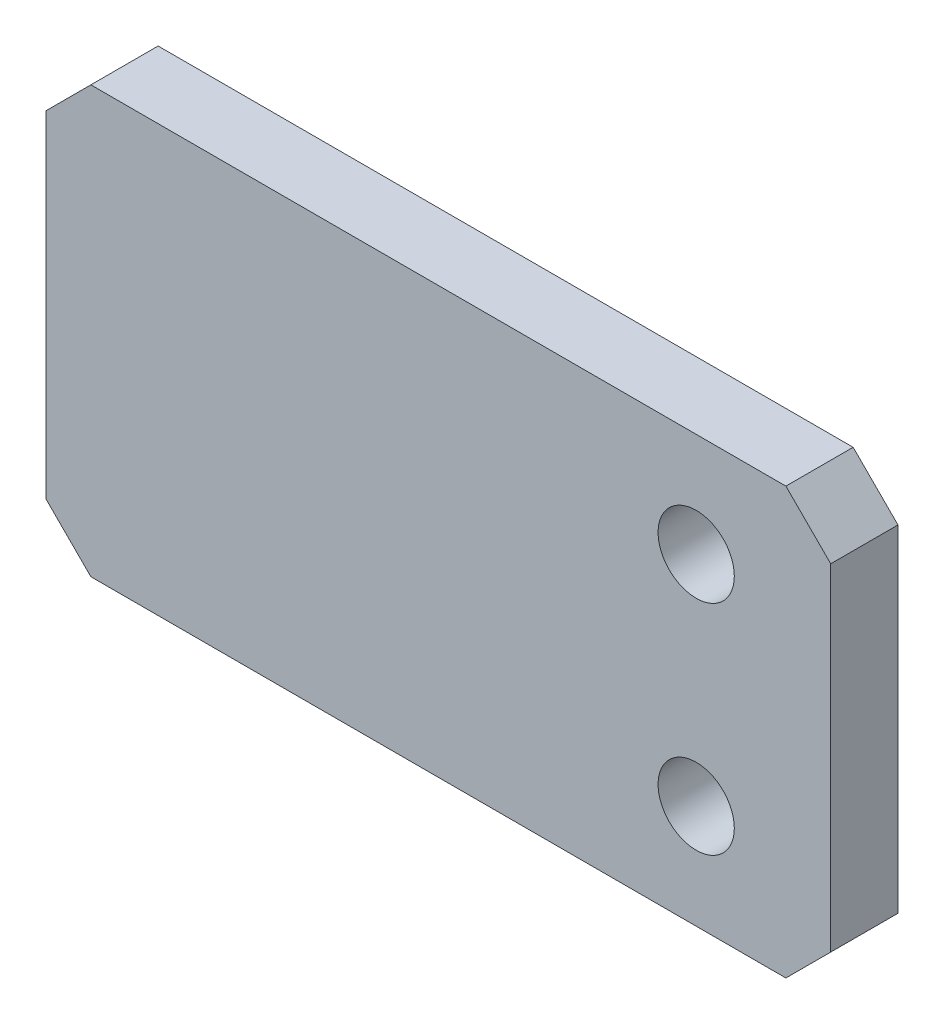
SolidWorks part; units mm, degrees
ref_plane "Front Plane" through (0, 0, 0) normal (0, 0, 1) x (1, 0, 0)
ref_plane "Top Plane" through (0, 0, 0) normal (0, 1, 0) x (1, 0, 0)
ref_plane "Right Plane" through (0, 0, 0) normal (1, 0, 0) x (0, 0, -1)
sketch "Sketch1" plane through (0, 0, 0) normal (0, 0, 1) x (1, 0, 0)
  line L1 (-17.5, -9.5) -> (17.5, -9.5)
  line L2 (-17.5, -9.5) -> (-17.5, 9.5)
  line L3 (-17.5, 9.5) -> (17.5, 9.5)
  line L4 (17.5, -9.5) -> (17.5, 9.5)
  line L5 (-17.5, -9.5) -> (17.5, 9.5) construction
  line L6 (-17.5, 9.5) -> (17.5, -9.5) construction
  point P0 (0, 0)
  dimension "D1" = 35
  dimension "D2" = 19
extrude "Boss-Extrude1" add sketch "Sketch1" along normal blind 3
chamfer "Chamfer1" distance 2 angle 45 4 edges at (-17.5, -9.5, 1.5) (17.5, -9.5, 1.5) (17.5, 9.5, 1.5) (-17.5, 9.5, 1.5)
hole_wizard "M3 Clearance Hole1" positions "Sketch3" profile "Sketch2" hole size "M3" standard "ISO" end condition up to next
sketch "Sketch3" plane through (0, 0, 3) normal (0, 0, 1) x (1, 0, 0)
  line L0 (17.5, -7.5) -> (17.5, 7.5) construction
  line L1 (17.5, 0) -> (-17.5, 0) construction
  line L2 (-17.5, 7.5) -> (-17.5, -7.5) construction
  point P0 (11.5, 4.8663)
  point P15 (11.5, -4.8663)
  dimension "D1" = 6
sketch "Sketch2" plane through (11.5, 4.8663, 3) normal (1, 0, 0) x (0, -1, 0)
  line L0 (0, 0) -> (0, 3)
  line L1 (0, 3) -> (1.7, 3)
  line L2 (1.7, 3) -> (1.7, 0)
  line L5 (1.7, 0) -> (0, 0)
  line L11 (0, -6.35) -> (0, 107.95) construction
  dimension "Thru Hole Dia." = 3.4
  dimension "Thru Hole Depth" = 3
